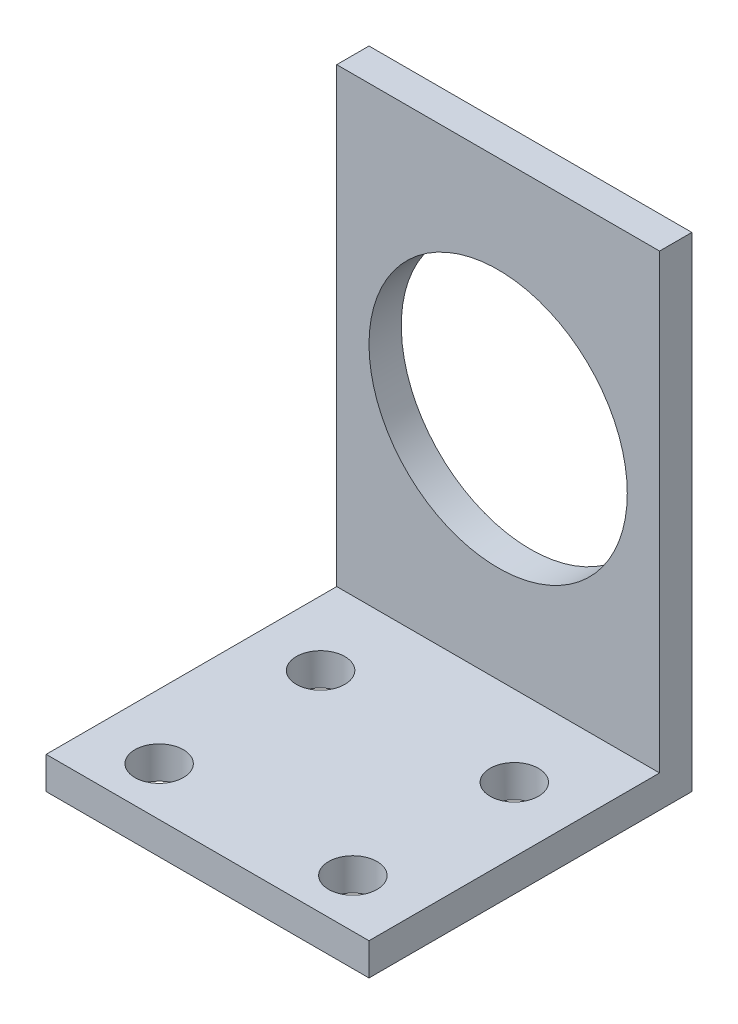
SolidWorks part; units mm, degrees
material "6063-O"
ref_plane "Front" through (0, 0, 0) normal (0, 0, 1) x (1, 0, 0)
ref_plane "Top" through (0, 0, 0) normal (0, 1, 0) x (1, 0, 0)
ref_plane "Right" through (0, 0, 0) normal (1, 0, 0) x (0, 0, -1)
sketch "草图1" plane through (0, 0, 0) normal (1, 0, 0) x (0, 0, -1)
  line L0 (0, 0) -> (0, 22)
  line L1 (0, 22) -> (3, 22)
  line L2 (3, 22) -> (3, -3)
  line L3 (3, -3) -> (-35, -3)
  line L4 (-35, -3) -> (-35, 0)
  line L5 (-35, 0) -> (0, 0)
  dimension "D1" = 22
  dimension "D2" = 3
  dimension "D3" = 25
  dimension "D4" = 38
extrude "凸台-拉伸1" add sketch "草图1" along normal blind 20
sketch "草图2" plane through (0, 0, 0) normal (0, 0, 1) x (1, 0, 0)
  line L0 (10, 22) -> (10, -3) construction
  line L1 (20, 22) -> (0, 22) construction
  line L2 (20, -3) -> (0, -3) construction
  circle A0 centre (10, 13) radius 8
  dimension "D1" = 16
  dimension "D2" = 9
extrude "切除-拉伸1" cut sketch "草图2" against normal up to next
sketch "草图3" plane through (0, 0, 0) normal (0, 1, 0) x (1, 0, 0)
  line L0 (10, 3) -> (10, -30.8482) construction
  line L1 (20, 3) -> (0, 3) construction
  circle A0 centre (4, -4) radius 1.5
  circle A1 centre (16, -4) radius 1.5
  dimension "D1" = 3
  dimension "D2" = 3
  dimension "D3" = 12
  dimension "D4" = 7
extrude "切除-拉伸2" cut sketch "草图3" against normal up to next
sketch "草图6" plane through (0, 22, 0) normal (0, 1, 0) x (1, 0, 0)
  line L1 (0, 3) -> (20, 3)
  line L2 (0, 3) -> (0, 0)
  line L3 (0, 0) -> (20, 0)
  line L4 (20, 3) -> (20, 0)
extrude "凸台-拉伸2" add sketch "草图6" along normal blind 5
sketch "草图8" plane through (0, 0, 0) normal (0, 0, 1) x (1, 0, 0)
  line L1 (0, 27) -> (20, 27)
  line L2 (0, 27) -> (0, 0)
  line L3 (0, 0) -> (20, 0)
  line L4 (20, 27) -> (20, 0)
extrude "切除-拉伸5" cut sketch "草图8" against normal blind 1
sketch "草图10" plane through (0, 0, 35) normal (0, 0, 1) x (1, 0, 0)
  line L1 (0, 0) -> (20, 0)
  line L2 (0, 0) -> (0, -3)
  line L3 (0, -3) -> (20, -3)
  line L4 (20, 0) -> (20, -3)
extrude "切除-拉伸7" cut sketch "草图10" against normal blind 18
sketch "草图11" plane through (0, 0, 0) normal (0, 1, 0) x (1, 0, 0)
  line L1 (20, 1) -> (0, 1)
  line L2 (20, 1) -> (20, -17)
  line L3 (20, -17) -> (0, -17)
  line L4 (0, 1) -> (0, -17)
extrude "切除-拉伸8" cut sketch "草图11" against normal blind 1
sketch "草图12" plane through (0, -1, 0) normal (0, 1, 0) x (1, 0, 0)
  line L0 (0, 1) -> (0, -17) construction
  line L1 (20, -17) -> (20, 1) construction
  line L2 (0, -17) -> (20, -17) construction
  circle A0 centre (4, -14) radius 1.5
  circle A1 centre (16, -14) radius 1.5
  dimension "D5" = 3
  dimension "D6" = 3
  dimension "D1" = 4
  dimension "D2" = 4
  dimension "D3" = 3
  dimension "D4" = 3
extrude "切除-拉伸9" cut sketch "草图12" against normal blind 2
